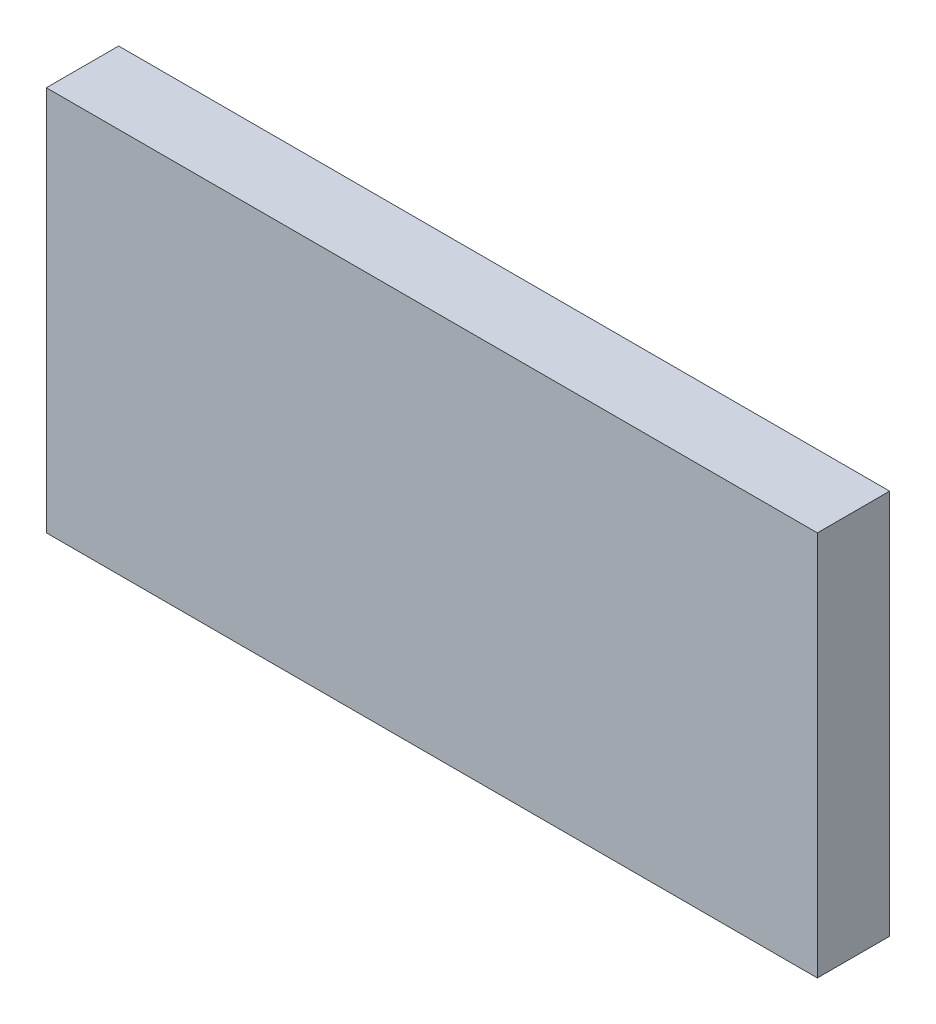
SolidWorks part; units mm, degrees
ref_plane "Plan de face" through (0, 0, 0) normal (0, 0, 1) x (1, 0, 0)
ref_plane "Plan de dessus" through (0, 0, 0) normal (0, 1, 0) x (1, 0, 0)
ref_plane "Plan de droite" through (0, 0, 0) normal (1, 0, 0) x (0, 0, -1)
sketch "Esquisse1" plane through (0, 0, 0) normal (0, 0, 1) x (1, 0, 0)
  line L1 (0, 0) -> (8, 0)
  line L2 (0, 0) -> (0, 4)
  line L3 (0, 4) -> (8, 4)
  line L4 (8, 0) -> (8, 4)
  dimension "D1" = 8
  dimension "D2" = 4
extrude "Extrusion1" add sketch "Esquisse1" along normal blind 0.75
